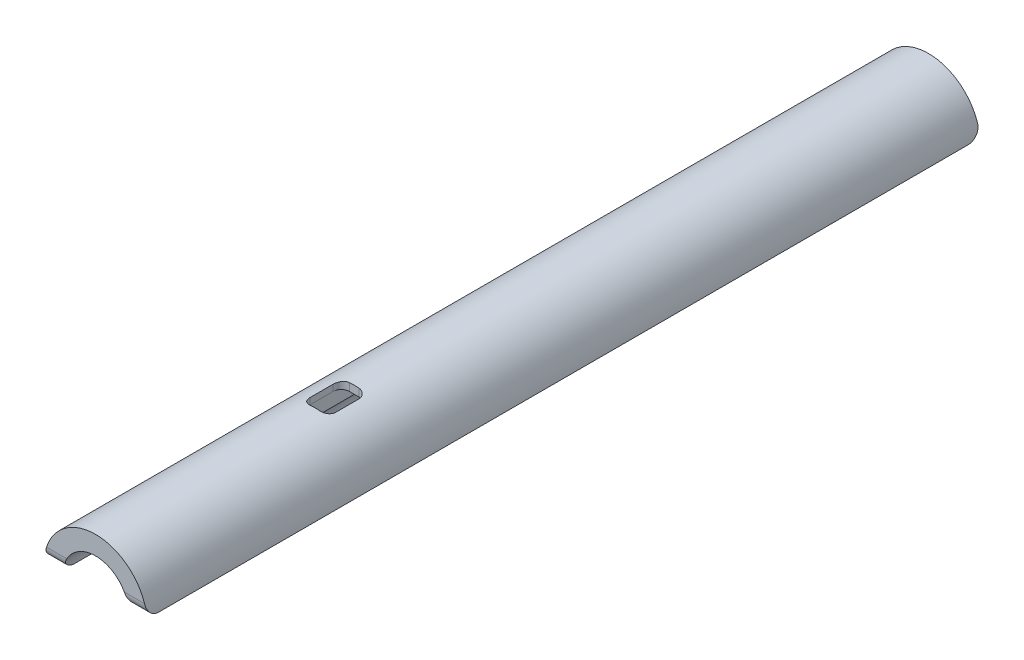
SolidWorks part; units mm, degrees
material "A-Glass Fiber"
ref_plane "Front Plane" through (0, 0, 0) normal (0, 0, 1) x (1, 0, 0)
ref_plane "Top Plane" through (0, 0, 0) normal (0, 1, 0) x (1, 0, 0)
ref_plane "Right Plane" through (0, 0, 0) normal (1, 0, 0) x (0, 0, -1)
sketch "Sketch1" plane through (0, 0, 0) normal (0, 0, 1) x (1, 0, 0)
  line L0 (40.7544, 5) -> (11.0867, 5) construction
  line L1 (-40.7544, 5) -> (-64.1454, 5)
  line L2 (0, 0) -> (0, -11.7162) construction
  line L3 (40.7544, 5) -> (64.1454, 5)
  arc A0 (40.7544, 5) -> (-40.7544, 5) centre (0, 0) ccw
  arc A2 (64.1454, 5) -> (-64.1454, 5) centre (0, 0) ccw
  dimension "D1" = 82.12
  dimension "D3" = 5
extrude "Boss-Extrude1" add sketch "Sketch1" along normal mid plane 1039
fillet "Fillet1" radius 15 4 edges at (-52.4499, 5, -519.5) (52.4499, 5, -519.5) (52.4499, 5, 519.5) (-52.4499, 5, 519.5)
ref_plane "Plane4" through (0, 0, 67) normal (0, 0, 1) x (1, 0, 0)
sketch "Sketch2" plane through (0, 0, 0) normal (0, 1, 0) x (1, 0, 0)
  line L0 (0, 0) -> (0, -107.6084) construction
  line L1 (16.5, -264) -> (-16.5, -264)
  line L2 (16.5, -264) -> (16.5, -62)
  line L3 (16.5, -62) -> (-16.5, -62)
  line L4 (-16.5, -264) -> (-16.5, -62)
  line L5 (16.5, -264) -> (-16.5, -62) construction
  line L6 (16.5, -62) -> (-16.5, -264) construction
  line L7 (0, 0) -> (133.0686, 0) construction
  point P0 (0, -163)
  dimension "D1" = 62
  dimension "D2" = 33
  dimension "D3" = 264
extrude "Cut-Extrude1" cut sketch "Sketch2" along normal blind 54.5
fillet "Fillet2" radius 10 4 edges at (-16.5, 46.0494, 62) (16.5, 46.0494, 62) (-16.5, 46.0494, 264) (16.5, 46.0494, 264)
sketch "Sketch3" plane through (0, 5, 0) normal (0, -1, 0) x (1, 0, 0)
  line L0 (-6.5, 264) -> (6.5, 264) construction
  line L1 (-5.9999, 246) -> (6.0001, 246)
  line L2 (-15.9999, 236) -> (-15.9999, 207)
  line L3 (-5.9999, 197) -> (6.0001, 197)
  line L4 (16.0001, 236) -> (16.0001, 207)
  line L5 (-64.1454, 504.5) -> (-64.1454, -504.5) construction
  arc A1 (6.0001, 246) -> (16.0001, 236) centre (6.0001, 236) cw
  arc A2 (16.0001, 207) -> (6.0001, 197) centre (6.0001, 207) cw
  arc A3 (-5.9999, 197) -> (-15.9999, 207) centre (-5.9999, 207) cw
  arc A4 (-15.9999, 236) -> (-5.9999, 246) centre (-5.9999, 236) cw
  point P15 (16.0001, 246)
  point P20 (-15.9999, 197)
  point P23 (-15.9999, 246)
  dimension "D5" = 10
  dimension "D1" = 32
  dimension "D2" = 49
  dimension "D3" = 18
  dimension "D4" = 48.1455
extrude "Cut-Extrude2" cut sketch "Sketch3" against normal through all
